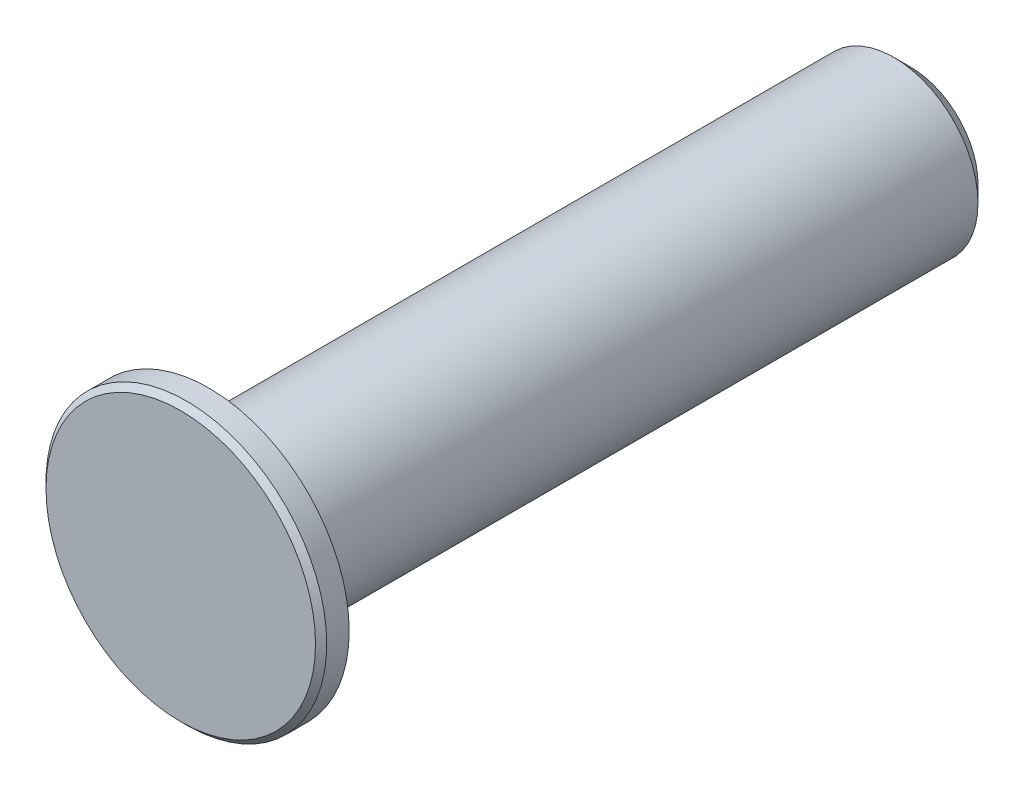
SolidWorks part; units mm, degrees
ref_plane "Front Plane" through (0, 0, 0) normal (0, 0, 1) x (1, 0, 0)
ref_plane "Top Plane" through (0, 0, 0) normal (0, 1, 0) x (1, 0, 0)
ref_plane "Right Plane" through (0, 0, 0) normal (1, 0, 0) x (0, 0, -1)
sketch "Sketch1" plane through (0, 0, 0) normal (0, 0, 1) x (1, 0, 0)
  circle A0 centre (0, 0) radius 3
  dimension "D1" = 6
extrude "Boss-Extrude1" add sketch "Sketch1" along normal blind 25
sketch "Sketch2" plane through (0, 0, 25) normal (0, 0, 1) x (1, 0, 0)
  circle A0 centre (0, 0) radius 5
  dimension "D1" = 10
extrude "Boss-Extrude2" add sketch "Sketch2" along normal blind 1
chamfer "Chamfer1" distance 0.6 angle 45 1 edges at (3, 0, 0)
chamfer "Chamfer2" distance 0.2 angle 45 1 edges at (5, 0, 26)
